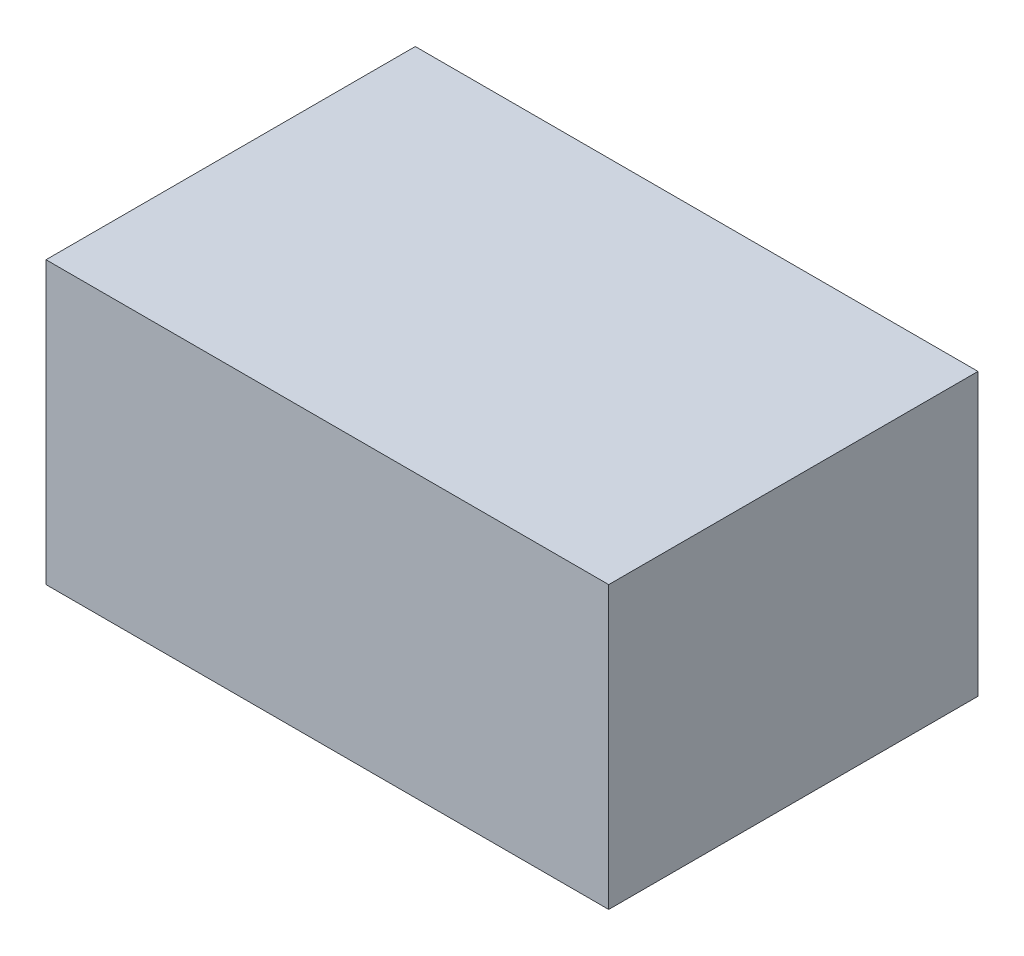
SolidWorks part; units mm, degrees
ref_plane "Front Plane" through (0, 0, 0) normal (0, 0, 1) x (1, 0, 0)
ref_plane "Top Plane" through (0, 0, 0) normal (0, 1, 0) x (1, 0, 0)
ref_plane "Right Plane" through (0, 0, 0) normal (1, 0, 0) x (0, 0, -1)
sketch "Sketch1" plane through (0, 0, 0) normal (0, 1, 0) x (1, 0, 0)
  line L1 (-101.6, -66.675) -> (101.6, -66.675)
  line L2 (-101.6, -66.675) -> (-101.6, 66.675)
  line L3 (-101.6, 66.675) -> (101.6, 66.675)
  line L4 (101.6, -66.675) -> (101.6, 66.675)
  line L5 (-101.6, -66.675) -> (101.6, 66.675) construction
  line L6 (-101.6, 66.675) -> (101.6, -66.675) construction
  point P0 (0, 0)
  dimension "D1" = 133.35
  dimension "D2" = 203.2
extrude "Boss-Extrude1" add sketch "Sketch1" along normal blind 101.6
